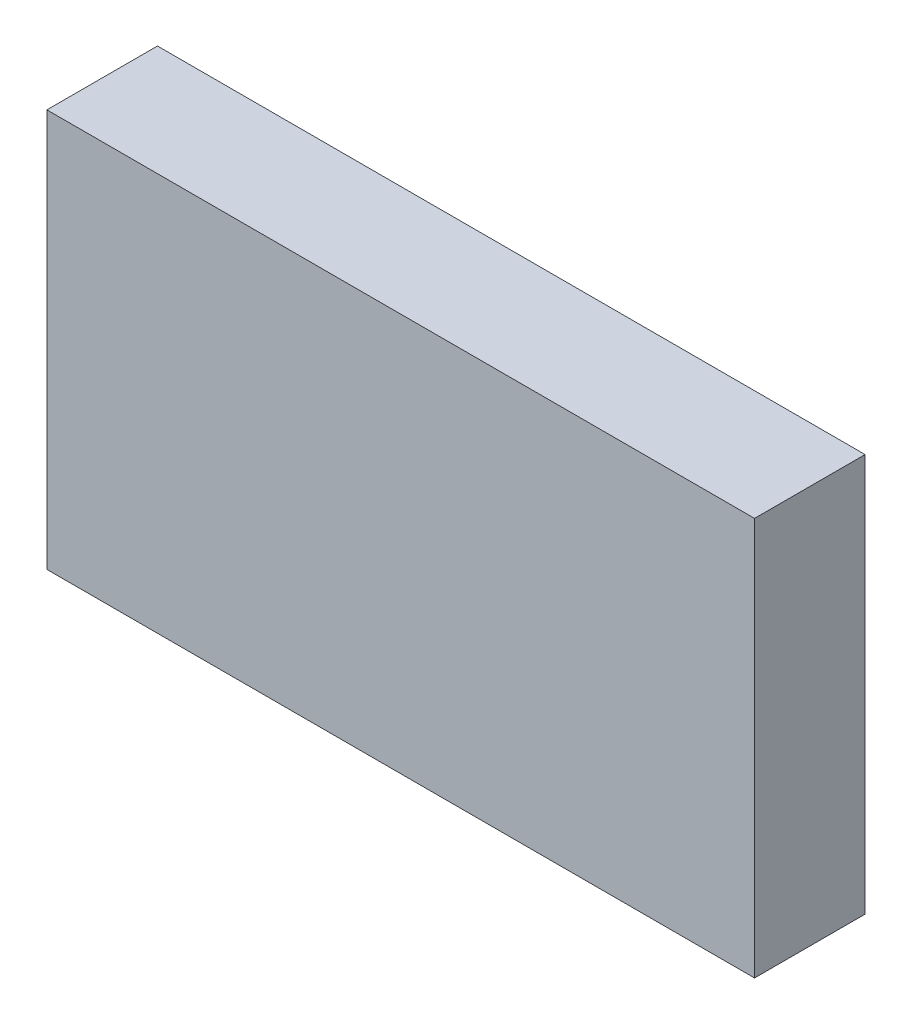
SolidWorks part; units mm, degrees
ref_plane "前基準面" through (0, 0, 0) normal (0, 0, 1) x (1, 0, 0)
ref_plane "上基準面" through (0, 0, 0) normal (0, 1, 0) x (1, 0, 0)
ref_plane "右基準面" through (0, 0, 0) normal (1, 0, 0) x (0, 0, -1)
sketch "草圖1" plane through (0, 0, 0) normal (0, 0, 1) x (1, 0, 0)
  line L1 (-16, 9) -> (16, 9)
  line L2 (-16, 9) -> (-16, -9)
  line L3 (-16, -9) -> (16, -9)
  line L4 (16, 9) -> (16, -9)
  line L5 (-16, 9) -> (16, -9) construction
  line L6 (-16, -9) -> (16, 9) construction
  point P0 (0, 0)
  dimension "D1" = 32
  dimension "D2" = 18
extrude "填料-伸長1" add sketch "草圖1" along normal blind 5
